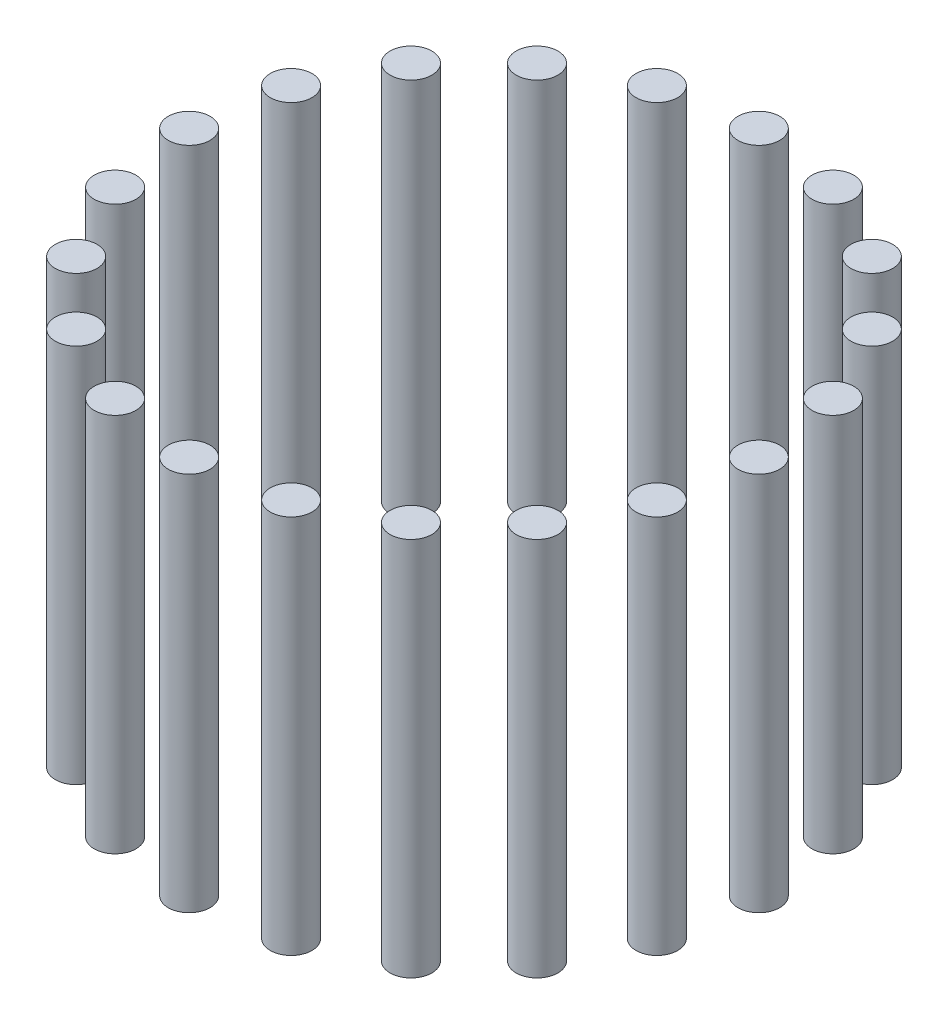
SolidWorks part; units mm, degrees
ref_plane "Front Plane" through (0, 0, 0) normal (0, 0, 1) x (1, 0, 0)
ref_plane "Top Plane" through (0, 0, 0) normal (0, 1, 0) x (1, 0, 0)
ref_plane "Right Plane" through (0, 0, 0) normal (1, 0, 0) x (0, 0, -1)
sketch "Sketch1" plane through (0, 0, 0) normal (0, 1, 0) x (1, 0, 0)
  circle A1 centre (0, 75) radius 5.5
  circle A2 centre (23.1763, 71.3292) radius 5.5
  circle A3 centre (44.0839, 60.6763) radius 5.5
  circle A4 centre (60.6763, 44.0839) radius 5.5
  circle A5 centre (71.3292, 23.1763) radius 5.5
  circle A6 centre (75, 0) radius 5.5
  circle A7 centre (71.3292, -23.1763) radius 5.5
  circle A8 centre (60.6763, -44.0839) radius 5.5
  circle A9 centre (44.0839, -60.6763) radius 5.5
  circle A10 centre (23.1763, -71.3292) radius 5.5
  circle A11 centre (0, -75) radius 5.5
  circle A12 centre (-23.1763, -71.3292) radius 5.5
  circle A13 centre (-44.0839, -60.6763) radius 5.5
  circle A14 centre (-60.6763, -44.0839) radius 5.5
  circle A15 centre (-71.3292, -23.1763) radius 5.5
  circle A16 centre (-75, 0) radius 5.5
  circle A17 centre (-71.3292, 23.1763) radius 5.5
  circle A18 centre (-60.6763, 44.0839) radius 5.5
  circle A19 centre (-44.0839, 60.6763) radius 5.5
  circle A20 centre (-23.1763, 71.3292) radius 5.5
  point P48 (0, 0)
  dimension "D1" = 20
extrude "Boss-Extrude1" add sketch "Sketch1" along normal blind 100
